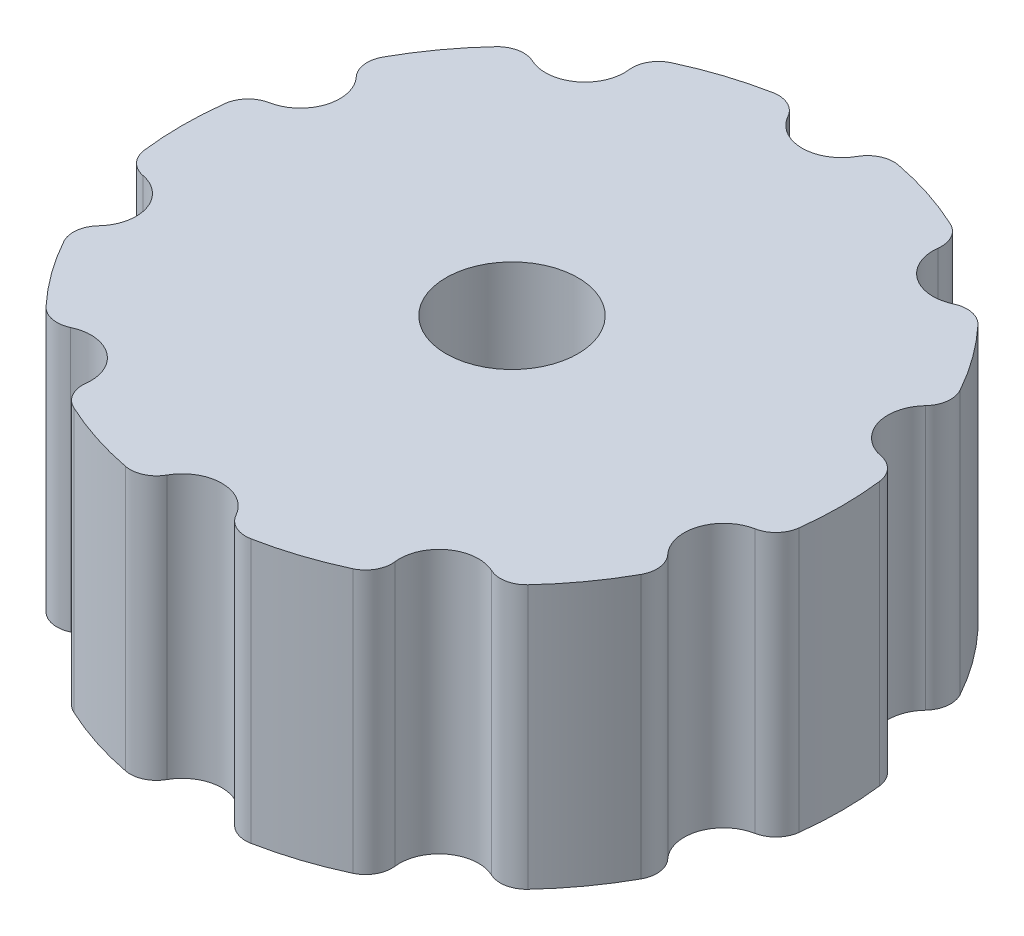
SolidWorks part; units mm, degrees
ref_plane "Plan de face" through (0, 0, 0) normal (0, 0, 1) x (1, 0, 0)
ref_plane "Plan de dessus" through (0, 0, 0) normal (0, 1, 0) x (1, 0, 0)
ref_plane "Plan de droite" through (0, 0, 0) normal (1, 0, 0) x (0, 0, -1)
sketch "Esquisse1" plane through (0, 0, 0) normal (0, 1, 0) x (1, 0, 0)
  circle A0 centre (0, 0) radius 12.5
  dimension "D1" = 25
extrude "Boss.-Extru.1" add sketch "Esquisse1" along normal blind 10
sketch "Esquisse3" plane through (0, 0, 0) normal (0, -1, 0) x (-1, 0, 0)
  circle A0 centre (0, -12.5) radius 1.5
  circle A2 centre (0, 0) radius 12.5 construction
  dimension "D1" = 3
extrude "Enlèv. mat.-Extru.1" cut sketch "Esquisse3" against normal blind 10
fillet "Congé1" radius 1 2 edges at (-1.4973, 5, 12.41) (1.4973, 5, 12.41)
pattern_circular "Répétition circulaire1" count 10 over 360 about axis through (0, 0, 0) along (0, 1, 0) of "Congé1", "Enlèv. mat.-Extru.1"
sketch "Esquisse4" plane through (0, 10, 0) normal (0, 1, 0) x (1, 0, 0)
  circle A0 centre (0, 0) radius 2.5
  dimension "D1" = 5
extrude "Enlèv. mat.-Extru.2" cut sketch "Esquisse4" against normal blind 10
